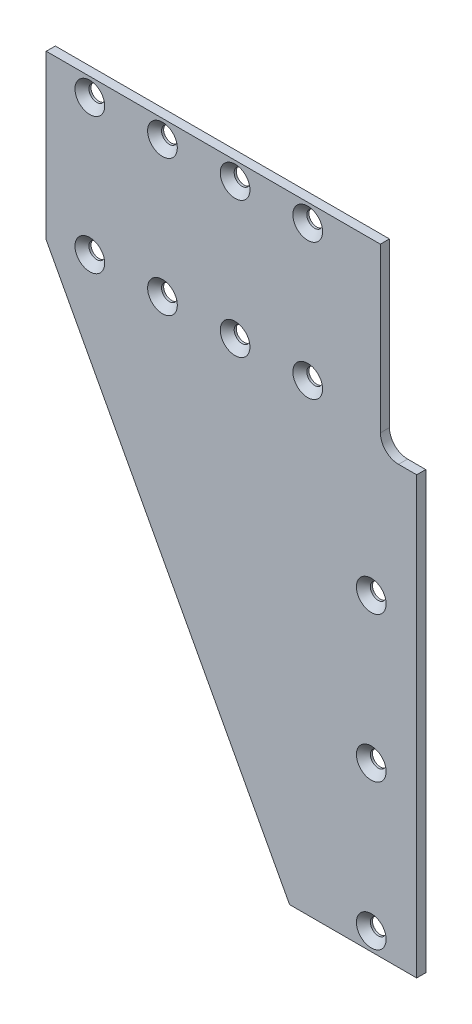
SolidWorks part; units mm, degrees
material "ASTM A36 Steel"
ref_plane "Front Plane" through (0, 0, 0) normal (0, 0, 1) x (1, 0, 0)
ref_plane "Top Plane" through (0, 0, 0) normal (0, 1, 0) x (1, 0, 0)
ref_plane "Right Plane" through (0, 0, 0) normal (1, 0, 0) x (0, 0, -1)
sketch "Sketch1" plane through (0, 0, 0) normal (0, 0, 1) x (1, 0, 0)
  line L0 (0, 0) -> (0, 152.4)
  line L1 (-12.7, 215.9) -> (-129.54, 215.9)
  line L2 (-129.54, 215.9) -> (-129.54, 158.75)
  line L3 (-129.54, 158.75) -> (-44.45, 0)
  line L4 (-44.45, 0) -> (0, 0)
  line L5 (-12.7, 215.9) -> (-12.7, 158.75)
  line L6 (-6.35, 152.4) -> (0, 152.4)
  arc A0 (-12.7, 158.75) -> (-6.35, 152.4) centre (-6.35, 158.75) ccw
  point P11 (-12.7, 152.4)
  dimension "D7" = 6.35
  dimension "D1" = 44.45
  dimension "D2" = 215.9
  dimension "D3" = 129.54
  dimension "D4" = 57.15
  dimension "D5" = 12.7
  dimension "D6" = 152.4
extrude "Boss-Extrude1" add sketch "Sketch1" against normal blind 3.175
sketch "Sketch2" plane through (0, 0, 0) normal (0, 0, 1) x (1, 0, 0)
  line L0 (-114.3, 209.55) -> (-38.1, 209.55) construction
  line L1 (-114.3, 161.925) -> (-38.1, 161.925) construction
  line L2 (-12.7, 215.9) -> (-129.54, 215.9) construction
  line L3 (-15.875, 6.35) -> (-15.875, 57.15) construction
  line L4 (-15.875, 57.15) -> (-15.875, 107.95) construction
  line L5 (-44.45, 0) -> (0, 0) construction
  line L6 (0, 0) -> (0, 152.4) construction
  line L7 (-12.7, 158.75) -> (-12.7, 215.9) construction
  dimension "D1" = 47.625
  dimension "D2" = 6.35
  dimension "D3" = 50.8
  dimension "D4" = 50.8
  dimension "D5" = 6.35
  dimension "D6" = 15.875
  dimension "D7" = 76.2
  dimension "D8" = 25.4
hole_wizard "CSK for #0 Flat Head Machine Screw (100)1" positions "3DSketch1" profile "Sketch3" countersink size "#0" standard "ANSI Inch" end condition through all
sketch3d "3DSketch1"
  point P0 (-114.3, 209.55, 0)
  point P3 (-114.3, 161.925, 0)
sketch "Sketch3" plane through (-114.3, 209.55, 0) normal (1, 0, 0) x (0, -1, 0)
  line L0 (0, 0) -> (0, 3.175)
  line L1 (0, 3.175) -> (2.7559, 3.175)
  line L2 (2.7559, 3.175) -> (2.7559, 2.4384)
  line L3 (2.7559, 2.4384) -> (5.1943, 0)
  line L5 (5.1943, 0) -> (0, 0)
  line L6 (-2.7559, 2.4384) -> (-5.1943, 0) construction
  line L11 (0, -6.35) -> (0, 107.95) construction
  dimension "Thru Hole Dia." = 5.5118
  dimension "Thru Hole Depth" = 3.175
  dimension "Near C'Sink Dia." = 10.3886
  dimension "Near C'Sink Angle" = 90
pattern_linear "LPattern1" count 4 spacing 25.4 along (1, 0, 0) of "CSK for #0 Flat Head Machine Screw (100)1"
hole_wizard "CSK for #0 Flat Head Machine Screw (100)2" positions "3DSketch2" profile "Sketch4" countersink size "#0" standard "ANSI Inch" end condition through all
sketch3d "3DSketch2"
  point P0 (-15.875, 107.95, 0)
sketch "Sketch4" plane through (-15.875, 107.95, 0) normal (1, 0, 0) x (0, -1, 0)
  line L0 (0, 0) -> (0, 3.175)
  line L1 (0, 3.175) -> (2.7559, 3.175)
  line L2 (2.7559, 3.175) -> (2.7559, 2.4384)
  line L3 (2.7559, 2.4384) -> (5.1943, 0)
  line L5 (5.1943, 0) -> (0, 0)
  line L6 (-2.7559, 2.4384) -> (-5.1943, 0) construction
  line L11 (0, -6.35) -> (0, 107.95) construction
  dimension "Thru Hole Dia." = 5.5118
  dimension "Thru Hole Depth" = 3.175
  dimension "Near C'Sink Dia." = 10.3886
  dimension "Near C'Sink Angle" = 90
pattern_linear "LPattern2" count 3 spacing 50.8 along (0, -1, 0) of "CSK for #0 Flat Head Machine Screw (100)2"
